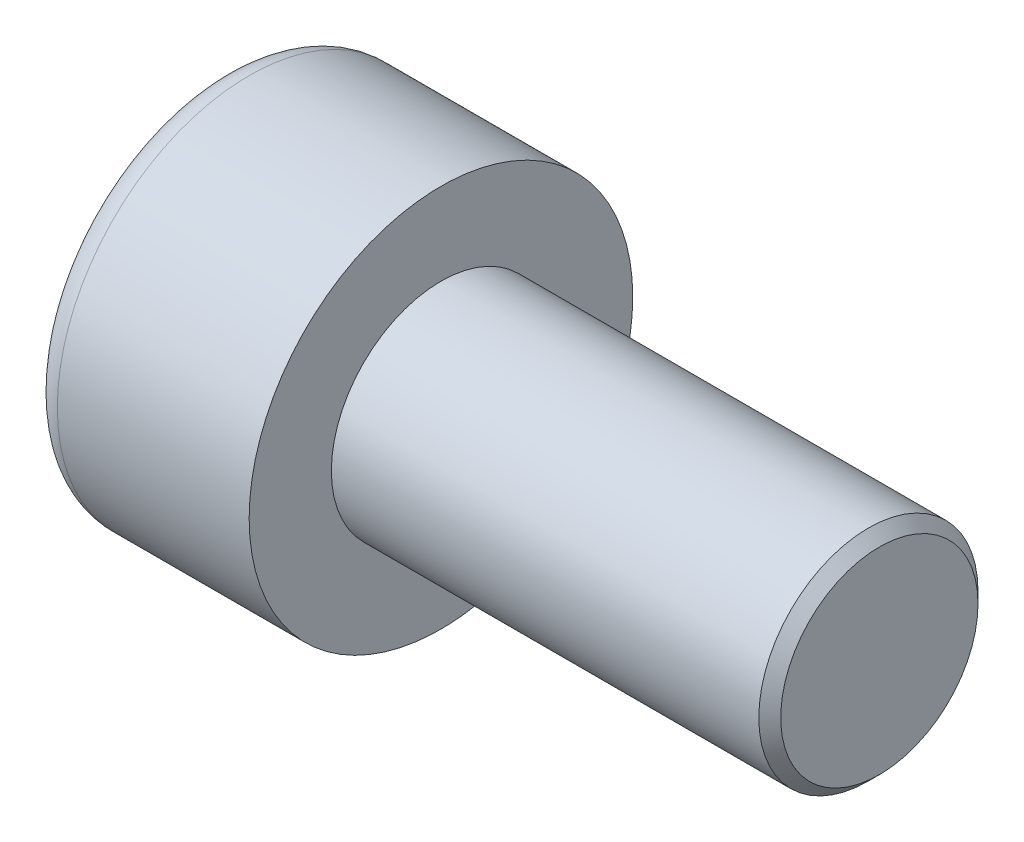
SolidWorks part; units mm, degrees
ref_plane "Front" through (0, 0, 0) normal (0, 0, 1) x (1, 0, 0)
ref_plane "Top" through (0, 0, 0) normal (0, 1, 0) x (1, 0, 0)
ref_plane "Right" through (0, 0, 0) normal (1, 0, 0) x (0, 0, -1)
sketch "Sketch1" plane through (0, 0, 0) normal (1, 0, 0) x (0, 0, -1)
  circle A0 centre (0, 0) radius 3.5
  dimension "dk" = 7
extrude "BaseHead" add sketch "Sketch1" along normal blind 4
sketch "Sketch2" plane through (4, 0, 0) normal (1, 0, 0) x (0, 0, -1)
  circle A0 centre (0, 0) radius 2
  dimension "d" = 4
extrude "BaseBody" add sketch "Sketch2" along normal blind 8
cosmetic thread "ThreadCosmetic1" [suppressed] parameters "b"=10, "D2"=3.242
sketch "Sketch3" plane through (0, 0, 0) normal (1, 0, 0) x (0, 0, -1)
  line L1 (1.7321, 0) -> (0.866, 1.5)
  line L2 (0.866, 1.5) -> (-0.866, 1.5)
  line L3 (-0.866, 1.5) -> (-1.7321, 0)
  line L4 (-1.7321, 0) -> (-0.866, -1.5)
  line L5 (-0.866, -1.5) -> (0.866, -1.5)
  line L6 (0.866, -1.5) -> (1.7321, 0)
  circle A0 centre (0, 0) radius 1.5 construction
  dimension "s" = 3
  dimension "e" = 3.4641
extrude "HexagonSocket" cut sketch "Sketch3" along normal blind 2
sketch "Sketch4" plane through (-4.1961, 0.75, 0) normal (0, 0, 1) x (-1, 0, 0)
  line L0 (-6.1961, 2.25) -> (-7.0622, 0.75)
  line L2 (-7.0622, 0.75) -> (-6.1961, 0.75)
  line L3 (-6.1961, 0.75) -> (-6.1961, 2.25)
  line L4 (-5.0351, 0.75) -> (0.839, 0.75) construction
  line L5 (-16.1961, 0.75) -> (-8.1961, 0.75) construction
  line L6 (-8.1961, 0.75) -> (-4.1961, 0.75) construction
  dimension "m" = 60
revolve "Cut-Revolve1" cut sketch "Sketch4" angle 360 about L4
fillet "HeadFillet" [suppressed] radius 0.2
fillet "TopFillet" radius 0.5 1 edges at (0, 0, -3.5)
chamfer "Chamfer1" distance 0.2 angle 45 1 edges at (12, 0, -2)
sketch "Sketch5" plane through (0, 0, 0) normal (0, 0, 1) x (1, 0, 0)
  line L0 (11.8, 1.6718) -> (11.9895, 2)
  line L1 (11.9895, 2) -> (11.9895, 2.379)
  line L2 (11.9895, 2.379) -> (11.6105, 2.379)
  line L3 (11.6105, 2.379) -> (11.6105, 2)
  line L4 (11.6105, 2) -> (11.8, 1.6718)
  line L5 (0, 0) -> (7.8886, 0) construction
  line L6 (11.8, -2) -> (11.8, 2) construction
  dimension "D1" = 4
  dimension "D2" = 0.379
revolve "Cut-Revolve10" [suppressed] cut sketch "Sketch5" angle 360 about L5
pattern_linear "LPattern10" [suppressed] count 22 spacing 0.4548 along (1, 0, 0)
equation "\"r1@TopFillet\" = \"d@Sketch2\" / 8"
equation "\"D1@Chamfer1\" = \"r@HeadFillet\""
equation "\"D1@Sketch5\" = \"d@Sketch2\""
equation "\"D2@Sketch5\" =  ( \"d@Sketch2\" - \"D2@ThreadCosmetic1\" )  / 2"
equation "\"D3@LPattern10\" = \"D2@Sketch5\" * 1.2"
equation "\"D1@LPattern10\" = \"b@ThreadCosmetic1\" / \"D3@LPattern10\""
